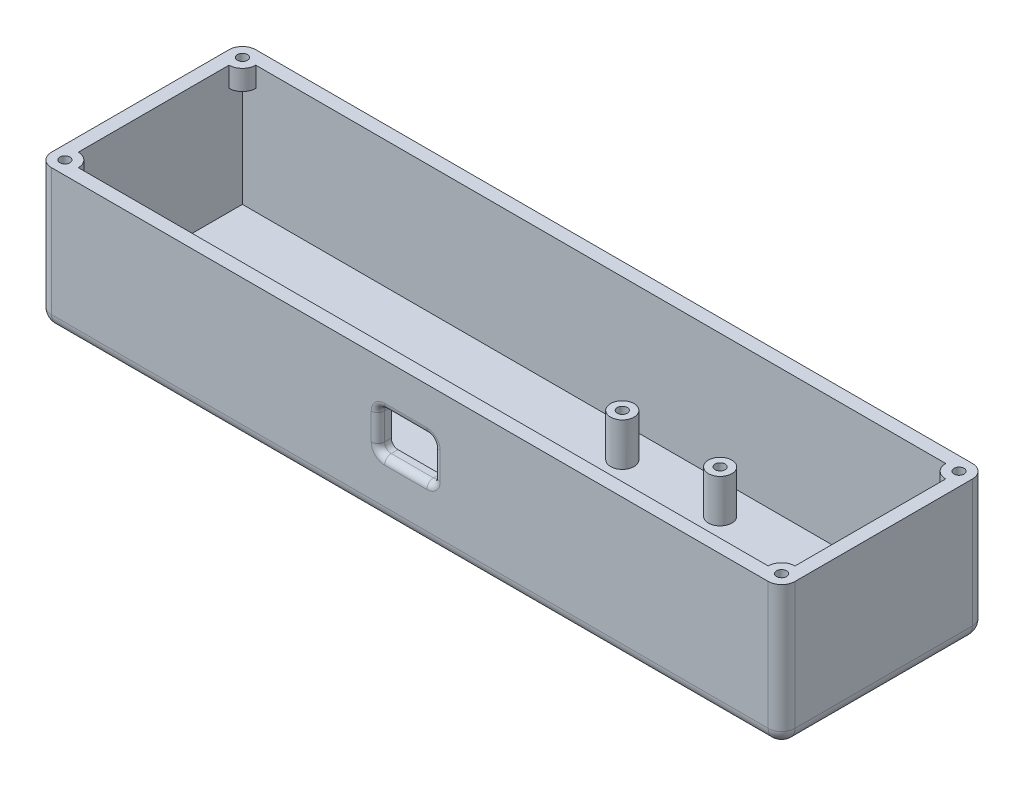
SolidWorks part; units mm, degrees
ref_plane "Front Plane" through (0, 0, 0) normal (0, 0, 1) x (1, 0, 0)
ref_plane "Top Plane" through (0, 0, 0) normal (0, 1, 0) x (1, 0, 0)
ref_plane "Right Plane" through (0, 0, 0) normal (1, 0, 0) x (0, 0, -1)
sketch "Sketch1" plane through (0, 0, 0) normal (0, 1, 0) x (1, 0, 0)
  line L1 (0, 0) -> (111, 0)
  line L2 (0, 0) -> (0, 30.5)
  line L3 (0, 30.5) -> (111, 30.5)
  line L4 (111, 0) -> (111, 30.5)
  dimension "D1" = 30.5
  dimension "D2" = 111
extrude "Boss-Extrude1" add sketch "Sketch1" along normal blind 2
sketch "Sketch2" plane through (0, 2, 0) normal (0, 1, 0) x (1, 0, 0)
  line L0 (2, 2) -> (109, 2)
  line L1 (0, 0) -> (111, 0)
  line L2 (0, 0) -> (0, 30.5)
  line L3 (0, 30.5) -> (111, 30.5)
  line L4 (111, 0) -> (111, 30.5)
  line L5 (109, 2) -> (109, 28.5)
  line L6 (2, 28.5) -> (109, 28.5)
  line L7 (2, 2) -> (2, 28.5)
  dimension "D1" = 2
extrude "Boss-Extrude2" add sketch "Sketch2" along normal blind 19
fillet "Fillet1" radius 2 8 edges at (55.5, 0, 0) (111, 0, -15.25) (55.5, 0, -30.5) (0, 0, -15.25) (111, 10.5, 0) (111, 10.5, -30.5) (0, 10.5, -30.5) (0, 10.5, 0)
sketch "Sketch4" plane through (0, 21, 0) normal (0, 1, 0) x (1, 0, 0)
  circle A0 centre (2, 28.5) radius 2
  circle A1 centre (2, 2) radius 2
  circle A2 centre (109, 2) radius 2
  circle A3 centre (109, 28.5) radius 2
extrude "Boss-Extrude4" add sketch "Sketch4" against normal blind 3
sketch "Sketch5" plane through (0, 2, 0) normal (0, 1, 0) x (1, 0, 0)
  line L0 (2, 15.25) -> (109, 15.25) construction
  line L1 (2, 26.5) -> (2, 4) construction
  line L2 (109, 4) -> (109, 26.5) construction
  line L3 (78, 23.825) -> (78, 6.675) construction
  circle A0 centre (63.39, 23.825) radius 0.75
  circle A1 centre (63.39, 23.825) radius 1.75
  circle A2 centre (63.39, 6.675) radius 0.75
  circle A3 centre (63.39, 6.675) radius 1.75
  circle A4 centre (78, 6.675) radius 0.75
  circle A5 centre (78, 6.675) radius 1.75
  circle A6 centre (78, 23.825) radius 0.75
  circle A7 centre (78, 23.825) radius 1.75
  point P18 (78, 15.25)
  dimension "D1" = 1.5
  dimension "D2" = 3.5
  dimension "D3" = 14.61
  dimension "D4" = 14.61
  dimension "D5" = 17.15
  dimension "D6" = 17.15
  dimension "D7" = 31
extrude "Boss-Extrude5" add sketch "Sketch5" along normal blind 6.4
sketch "Sketch6" plane through (0, 0, 0) normal (0, 0, 1) x (1, 0, 0)
  line L0 (63.39, 8.4) -> (63.39, 21) construction
  line L1 (64.14, 8.4) -> (62.64, 8.4) construction
  line L2 (2, 21) -> (109, 21) construction
  line L3 (63.39, 8.4) -> (63.39, 2) construction
  line L4 (2, 2) -> (109, 2) construction
  line L5 (50.73, 8.4) -> (59.03, 14.4) construction
  line L6 (50.73, 14.4) -> (59.03, 14.4)
  line L7 (50.73, 14.4) -> (50.73, 8.4)
  line L8 (50.73, 8.4) -> (59.03, 8.4)
  line L9 (59.03, 14.4) -> (59.03, 8.4)
  point P13 (54.88, 11.4)
  dimension "D1" = 8.51
  dimension "D2" = 8.3
  dimension "D3" = 6
  dimension "D4" = 0
extrude "Cut-Extrude1" cut sketch "Sketch6" against normal up to surface (2 mm away) up to face at (55.5, 14.75, -2)
fillet "Fillet2" radius 1 4 edges at (59.03, 14.4, -1) (50.73, 14.4, -1) (50.73, 8.4, -1) (59.03, 8.4, -1)
sketch "Sketch7" plane through (0, 21, 0) normal (0, 1, 0) x (1, 0, 0)
  circle A0 centre (2, 28.5) radius 0.75
  circle A1 centre (2, 2) radius 0.75
  circle A2 centre (109, 2) radius 0.75
  circle A3 centre (109, 28.5) radius 0.75
  dimension "D1" = 1.5
extrude "Cut-Extrude3" cut sketch "Sketch7" against normal blind 2.5
fillet "Fillet3" radius 1 8 edges at (58.7371, 14.1071, 0) (54.88, 14.4, 0) (51.0229, 14.1071, 0) (50.73, 11.4, 0) (51.0229, 8.6929, 0) (54.88, 8.4, 0) (58.7371, 8.6929, 0) (59.03, 11.4, 0)
